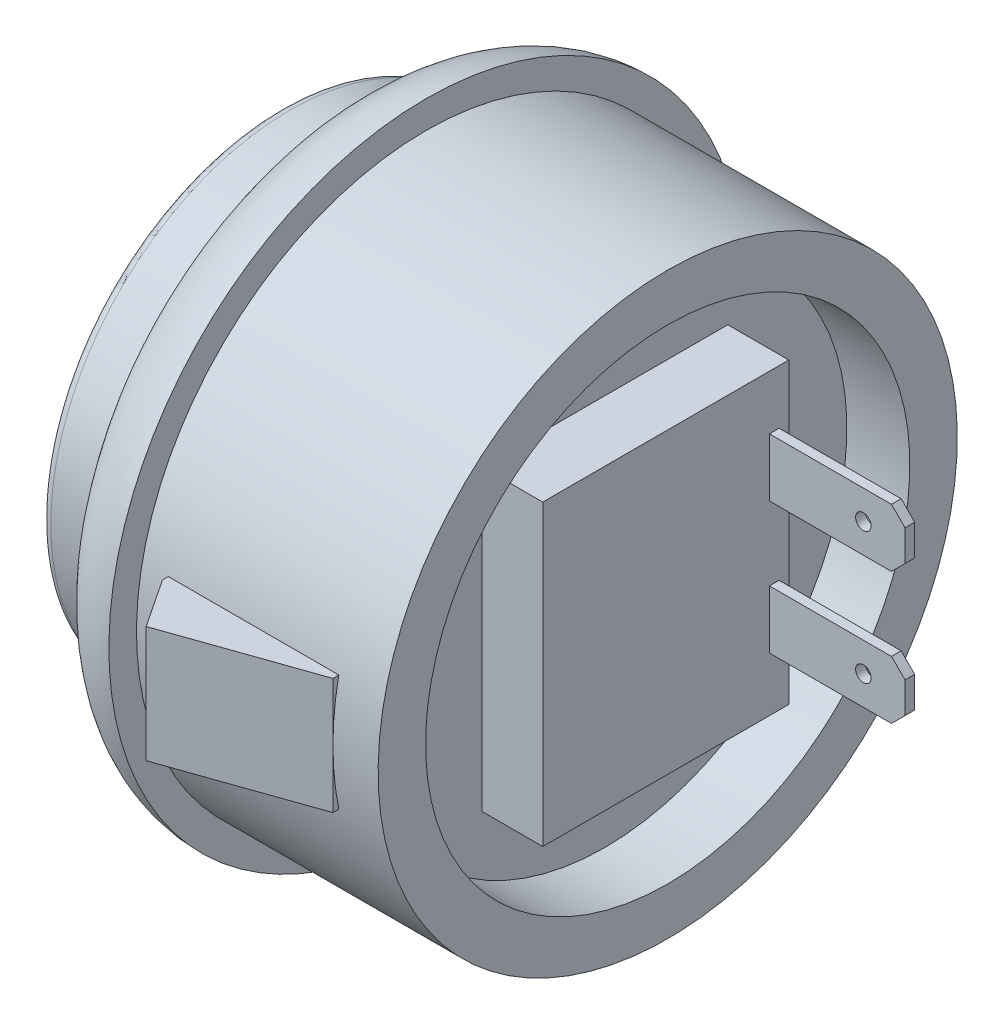
SolidWorks part; units mm, degrees
ref_plane "Front Plane" through (0, 0, 0) normal (0, 0, 1) x (1, 0, 0)
ref_plane "Top Plane" through (0, 0, 0) normal (0, 1, 0) x (1, 0, 0)
ref_plane "Right Plane" through (0, 0, 0) normal (1, 0, 0) x (0, 0, -1)
sketch "Sketch1" plane through (0, 0, 0) normal (0, 0, 1) x (1, 0, 0)
  line L0 (0, 0) -> (0, 12.35)
  line L1 (0, 12.35) -> (3.5, 12.35)
  line L2 (7.525, 16.375) -> (7.525, 14.95)
  line L3 (7.525, 14.95) -> (20, 14.95)
  line L4 (20, 14.95) -> (20, 12.5)
  line L5 (16.75, 0) -> (0, 0)
  line L6 (0, 0) -> (-7.0673, 0) construction
  line L7 (3.5, 12.35) -> (3.5, 11.4605) construction
  line L8 (7.525, 16.375) -> (8.9863, 16.375) construction
  line L9 (20, 12.5) -> (16.75, 12.5)
  line L10 (16.75, 12.5) -> (16.75, 0)
  arc A0 (7.525, 16.375) -> (3.5, 12.35) centre (7.525, 12.35) ccw
  dimension "D1" = 29.9
  dimension "D2" = 24.7
  dimension "D3" = 20
  dimension "D4" = 32.75
  dimension "D5" = 3.5
  dimension "D6" = 3.25
  dimension "D7" = 25
revolve "Revolve1" add sketch "Sketch1" angle 360 about L5
sketch "Sketch2" plane through (16.75, 0, 0) normal (1, 0, 0) x (0, 0, -1)
  line L1 (-6.35, 7.7) -> (6.35, 7.7)
  line L2 (-6.35, 7.7) -> (-6.35, -7.7)
  line L3 (-6.35, -7.7) -> (6.35, -7.7)
  line L4 (6.35, 7.7) -> (6.35, -7.7)
  line L5 (-6.35, 7.7) -> (6.35, -7.7) construction
  line L6 (-6.35, -7.7) -> (6.35, 7.7) construction
  point P0 (0, 0)
  dimension "D1" = 12.7
  dimension "D2" = 15.4
extrude "Boss-Extrude1" add sketch "Sketch2" along normal blind 3.15
sketch "Sketch3" plane through (19.9, 0, 0) normal (1, 0, 0) x (0, 0, -1)
  line L0 (0, 0) -> (5.2728, 0) construction
  line L1 (5.35, 4.9) -> (5.85, 4.9)
  line L2 (5.35, 4.9) -> (5.35, 1.9)
  line L3 (5.35, 1.9) -> (5.85, 1.9)
  line L4 (5.85, 4.9) -> (5.85, 1.9)
  line L5 (5.35, -1.9) -> (5.85, -1.9)
  line L6 (5.35, -1.9) -> (5.35, -4.9)
  line L7 (5.35, -4.9) -> (5.85, -4.9)
  line L8 (5.85, -1.9) -> (5.85, -4.9)
  line L9 (6.35, -7.7) -> (6.35, 7.7) construction
  dimension "D1" = 0.5
  dimension "D2" = 3
  dimension "D3" = 3.8
  dimension "D4" = 0.5
extrude "Boss-Extrude2" add sketch "Sketch3" along normal blind 7
sketch "Sketch4" plane through (0, 0, -5.85) normal (0, 0, -1) x (-1, 0, 0)
  line L0 (-26.9, 1.9) -> (-26.9, 4.9) construction
  line L1 (-26.9, -4.9) -> (-26.9, -1.9) construction
  circle A0 centre (-24.75, 3.4) radius 0.4
  circle A1 centre (-24.75, -3.4) radius 0.4
  point P8 (-26.9, 3.4)
  point P12 (-26.9, -3.4)
  dimension "D1" = 0.8
  dimension "D2" = 2.15
extrude "Cut-Extrude1" cut sketch "Sketch4" against normal through all
chamfer "Chamfer1" distance 0.7 angle 45 4 edges at (26.9, -4.9, -5.6) (26.9, -1.9, -5.6) (26.9, 1.9, -5.6) (26.9, 4.9, -5.6)
sketch "Sketch5" plane through (0, 0, 0) normal (0, 1, 0) x (1, 0, 0)
  line L0 (17.6667, -14.95) -> (10.525, -17.45)
  line L1 (7.525, -14.95) -> (20, -14.95) construction
  line L2 (10.525, -17.45) -> (8.8667, -14.95)
  line L3 (7.525, -14.95) -> (20, -14.95) construction
  line L4 (0, 0) -> (-5.0022, 0) construction
  line L5 (8.8667, 13.95) -> (8.8667, 14.95)
  line L6 (17.6667, 13.95) -> (8.8667, 13.95)
  line L7 (17.6667, -14.95) -> (17.6667, -13.95)
  line L8 (17.6667, -13.95) -> (8.8667, -13.95)
  line L9 (8.8667, -13.95) -> (8.8667, -14.95)
  line L10 (7.525, -16.375) -> (7.525, 16.375) construction
  line L11 (17.6667, 14.95) -> (17.6667, 13.95)
  line L12 (10.525, 17.45) -> (8.8667, 14.95)
  line L13 (17.6667, 14.95) -> (10.525, 17.45)
  dimension "D1" = 2.5
  dimension "D2" = 8.8
  dimension "D3" = 3
  dimension "D4" = 3
  dimension "D5" = 1
extrude "Boss-Extrude3" add sketch "Sketch5" along normal mid plane 6
fillet "Fillet1" radius 0.5 1 edges at (0, 12.35, 0)
